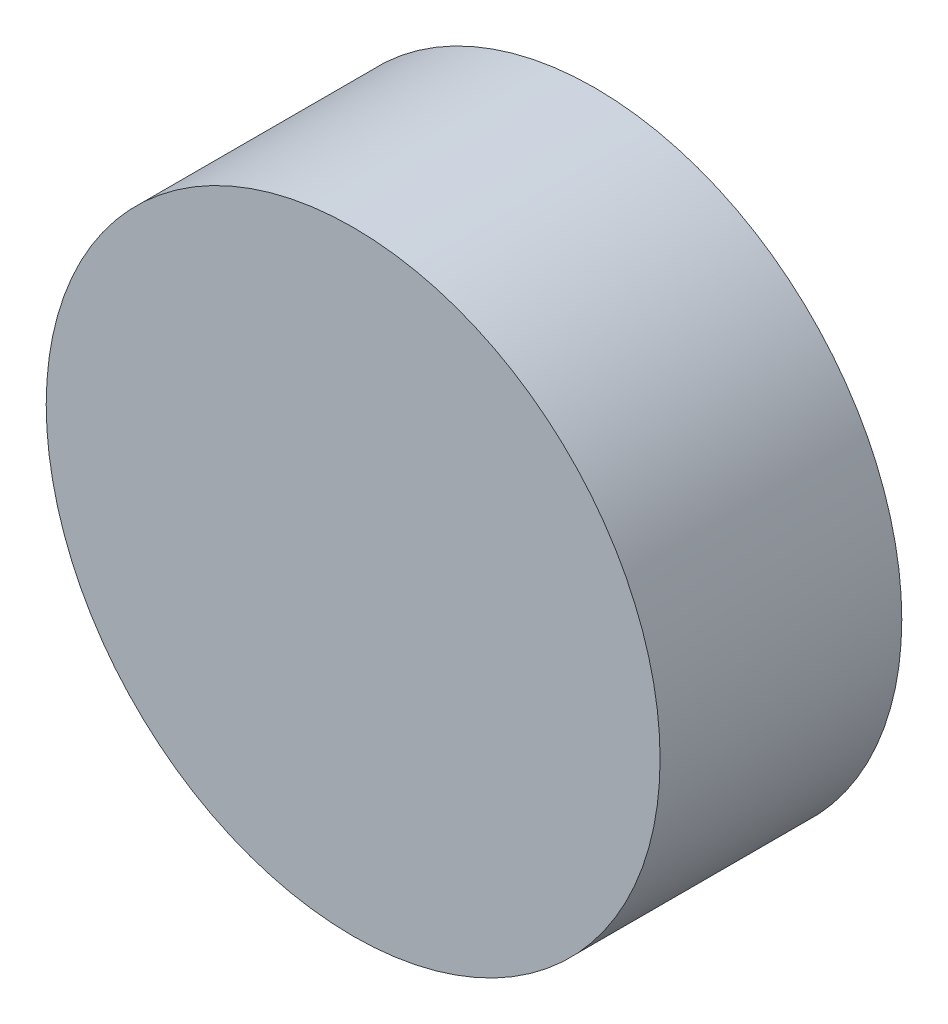
SolidWorks part; units mm, degrees
ref_plane "Alzado" through (0, 0, 0) normal (0, 0, 1) x (1, 0, 0)
ref_plane "Planta" through (0, 0, 0) normal (0, 1, 0) x (1, 0, 0)
ref_plane "Vista lateral" through (0, 0, 0) normal (1, 0, 0) x (0, 0, -1)
sketch "Croquis1" plane through (0, 0, 0) normal (0, 0, 1) x (1, 0, 0)
  circle A0 centre (0, 0) radius 101.6
  dimension "D1" = 203.2
extrude "Saliente-Extruir1" add sketch "Croquis1" along normal mid plane 80
